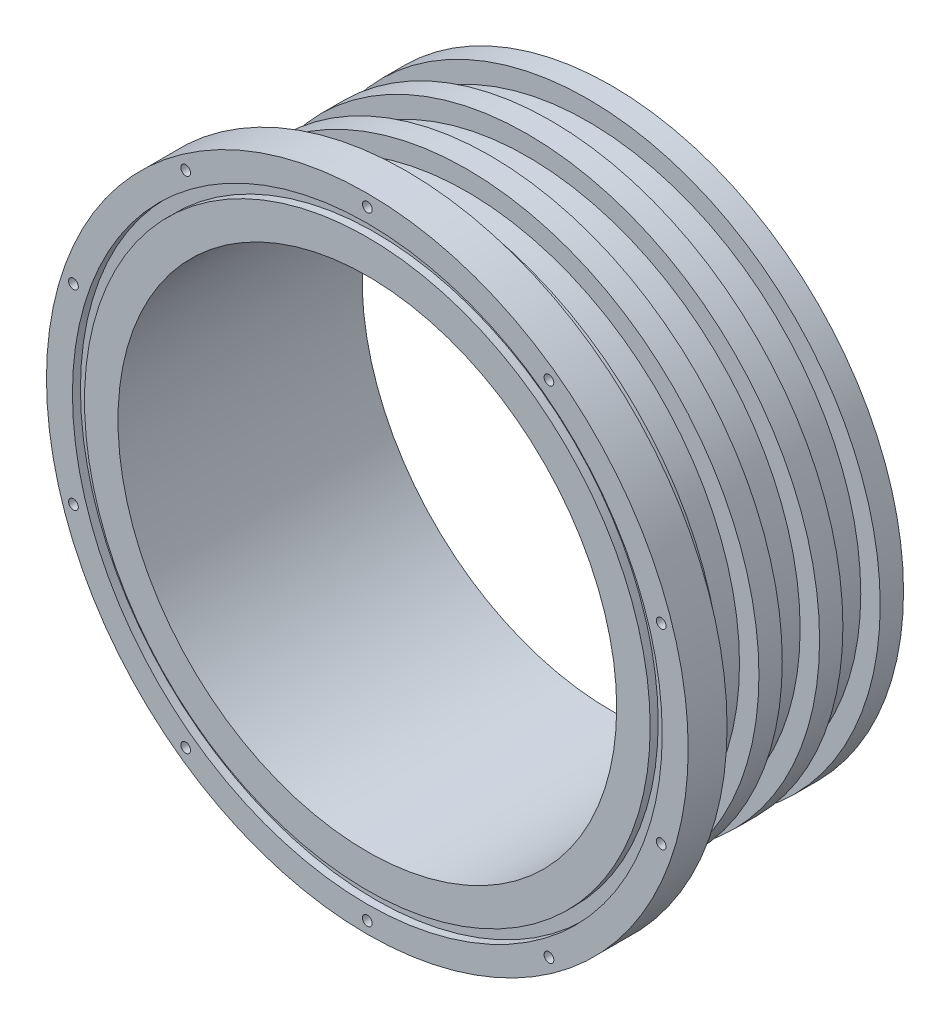
SolidWorks part; units mm, degrees
material "1060 Alloy"
ref_plane "Front Plane" through (0, 0, 0) normal (0, 0, 1) x (1, 0, 0)
ref_plane "Top Plane" through (0, 0, 0) normal (0, 1, 0) x (1, 0, 0)
ref_plane "Right Plane" through (0, 0, 0) normal (1, 0, 0) x (0, 0, -1)
sketch "Sketch1" plane through (0, 0, 0) normal (0, 1, 0) x (1, 0, 0)
  line L0 (-82.55, 0) -> (-82.55, 10)
  line L1 (-82.55, 10) -> (-75.15, 10)
  line L2 (-75.15, 10) -> (-75.15, 16)
  line L3 (-75.15, 16) -> (-70.15, 16)
  line L4 (-70.15, 16) -> (-70.15, 25.6)
  line L5 (-70.15, 25.6) -> (-75.15, 25.6)
  line L6 (-75.15, 25.6) -> (-75.15, 31.6)
  line L7 (-75.15, 31.6) -> (-70.15, 31.6)
  line L8 (-70.15, 31.6) -> (-70.15, 41.2)
  line L9 (-70.15, 41.2) -> (-75.15, 41.2)
  line L10 (-75.15, 41.2) -> (-75.15, 47.2)
  line L11 (-75.15, 47.2) -> (-70.15, 47.2)
  line L12 (-70.15, 47.2) -> (-70.15, 56.8)
  line L13 (-70.15, 56.8) -> (-75.15, 56.8)
  line L14 (-75.15, 56.8) -> (-75.15, 62.8)
  line L15 (-75.15, 62.8) -> (-64.15, 62.8)
  line L16 (-64.15, 62.8) -> (-64.15, 0)
  line L17 (-64.15, 0) -> (-82.55, 0)
  line L18 (0, 0) -> (0, 101.8418) construction
  dimension "D1" = 9.6
  dimension "D2" = 6
  dimension "D3" = 70.15
  dimension "D4" = 75.15
  dimension "D5" = 10
  dimension "D6" = 6
  dimension "D7" = 82.55
  dimension "D8" = 6
revolve "Revolve1" add sketch "Sketch1" angle 360 about L18
sketch "Sketch2" plane through (0, 0, 0) normal (0, 0, 1) x (1, 0, 0)
  circle A0 centre (0, 0) radius 79.5 construction
  point P3 (0, 79.5)
  point P7 (46.7289, 64.3169)
  point P8 (75.609, 24.5669)
  point P9 (75.609, -24.5669)
  point P10 (46.7289, -64.3169)
  point P11 (0, -79.5)
  point P12 (-46.7289, -64.3169)
  point P13 (-75.609, -24.5669)
  point P14 (-75.609, 24.5669)
  point P15 (-46.7289, 64.3169)
  point P16 (0, 0)
  dimension "D1" = 159
  dimension "D2" = 10
hole_wizard "M3x0.5 Tapped Hole1" positions "Sketch3" profile "Sketch4" tap size "M3x0.5" standard "ANSI Metric" end condition through all
sketch "Sketch3" plane through (0, 0, 0) normal (0, 0, 1) x (1, 0, 0)
  point P0 (0, 79.5)
  point P3 (46.7289, 64.3169)
  point P6 (75.609, 24.5669)
  point P9 (75.609, -24.5669)
  point P12 (46.7289, -64.3169)
  point P15 (0, -79.5)
  point P18 (-46.7289, -64.3169)
  point P21 (-75.609, -24.5669)
  point P24 (-75.609, 24.5669)
  point P27 (-46.7289, 64.3169)
sketch "Sketch4" plane through (0, 79.5, 0) normal (1, 0, 0) x (0, -1, 0)
  line L0 (0, 0) -> (0, 62.8)
  line L1 (0, 62.8) -> (1.25, 62.8)
  line L2 (1.25, 62.8) -> (1.25, 0)
  line L5 (1.25, 0) -> (0, 0)
  line L11 (0, -6.35) -> (0, 107.95) construction
  dimension "Thru Tap Drill Dia." = 2.5
  dimension "Thru Tap Drill Depth" = 62.8
cosmetic thread "Hole Thread1" parameters "D2"=3
cosmetic thread "Hole Thread2" parameters "D2"=3
cosmetic thread "Hole Thread3" parameters "D2"=3
cosmetic thread "Hole Thread4" parameters "D2"=3
cosmetic thread "Hole Thread5" parameters "D2"=3
cosmetic thread "Hole Thread6" parameters "D2"=3
cosmetic thread "Hole Thread7" parameters "D2"=3
cosmetic thread "Hole Thread8" parameters "D2"=3
cosmetic thread "Hole Thread9" parameters "D2"=3
cosmetic thread "Hole Thread10" parameters "D2"=3
sketch "Sketch5" plane through (0, 0, 0) normal (0, 0, 1) x (1, 0, 0)
  circle A0 centre (0, 0) radius 75.87
  circle A1 centre (0, 0) radius 72.77
  dimension "D1" = 151.74
  dimension "D2" = 145.54
extrude "Cut-Extrude1" cut sketch "Sketch5" against normal blind 2.06
equation "\"D7@Sketch1\"=76.20 + (6.35)"
